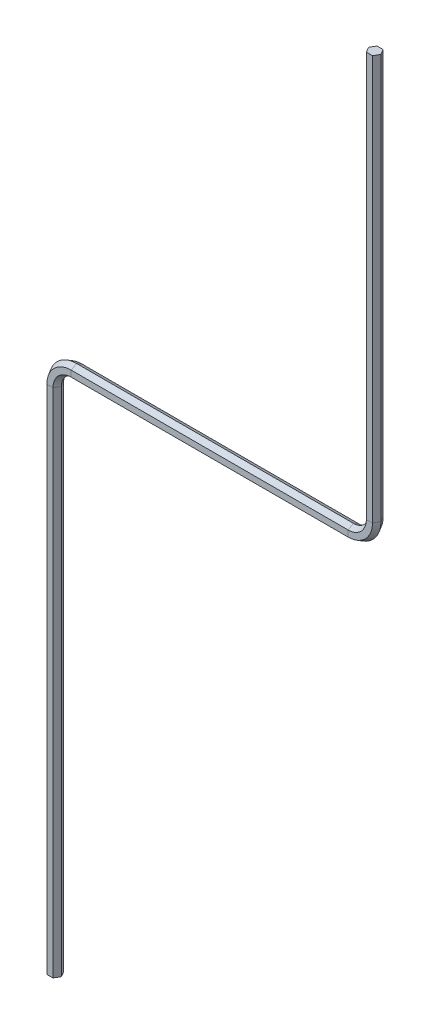
SolidWorks part; units mm, degrees
ref_plane "Front Plane" through (0, 0, 0) normal (0, 0, 1) x (1, 0, 0)
ref_plane "Top Plane" through (0, 0, 0) normal (0, 1, 0) x (1, 0, 0)
ref_plane "Right Plane" through (0, 0, 0) normal (1, 0, 0) x (0, 0, -1)
sketch "Sketch2" plane through (0, 0, 0) normal (0, 0, 1) x (1, 0, 0)
  line L0 (0, 0) -> (0, 480)
  line L1 (20, 500) -> (280, 500)
  line L2 (300, 520) -> (300, 900)
  arc A0 (280, 500) -> (300, 520) centre (280, 520) ccw
  arc A1 (0, 480) -> (20, 500) centre (20, 480) cw
  point P7 (300, 500)
  point P10 (0, 500)
  dimension "D4" = 20
  dimension "D1" = 500
  dimension "D2" = 400
  dimension "D3" = 300
sketch "Sketch3" plane through (0, 0, 0) normal (0, 1, 0) x (1, 0, 0)
  line L1 (2.8868, 5) -> (-2.8868, 5)
  line L2 (-2.8868, 5) -> (-5.7735, 0)
  line L3 (-5.7735, 0) -> (-2.8868, -5)
  line L4 (-2.8868, -5) -> (2.8868, -5)
  line L5 (2.8868, -5) -> (5.7735, 0)
  line L6 (5.7735, 0) -> (2.8868, 5)
  circle A0 centre (0, 0) radius 5 construction
  dimension "D1" = 10
sweep "Sweep3" add profiles "Sketch3" path "Sketch2"
